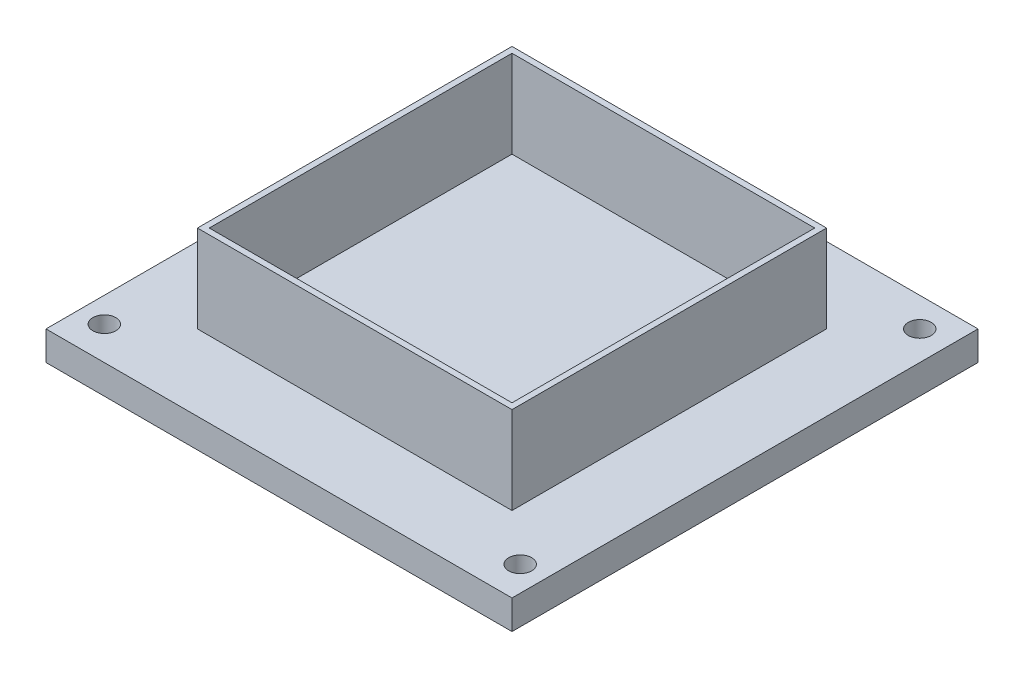
SolidWorks part; units mm, degrees
material "ABS_rapid_prototype"
ref_plane "Front" through (0, 0, 0) normal (0, 0, 1) x (1, 0, 0)
ref_plane "Top" through (0, 0, 0) normal (0, 1, 0) x (1, 0, 0)
ref_plane "Right" through (0, 0, 0) normal (1, 0, 0) x (0, 0, -1)
sketch "Sketch1" plane through (0, 0, 0) normal (0, 1, 0) x (1, 0, 0)
  line L1 (-50.8, 50.8) -> (50.8, 50.8)
  line L2 (-50.8, 50.8) -> (-50.8, -50.8)
  line L3 (-50.8, -50.8) -> (50.8, -50.8)
  line L4 (50.8, 50.8) -> (50.8, -50.8)
  line L5 (-50.8, 50.8) -> (50.8, -50.8) construction
  line L6 (-50.8, -50.8) -> (50.8, 50.8) construction
  line L7 (-38.1, 38.1) -> (38.1, 38.1)
  line L8 (-38.1, 38.1) -> (-38.1, -38.1)
  line L9 (-38.1, -38.1) -> (38.1, -38.1)
  line L10 (38.1, 38.1) -> (38.1, -38.1)
  line L11 (-38.1, 38.1) -> (38.1, -38.1) construction
  line L12 (-38.1, -38.1) -> (38.1, 38.1) construction
  line L13 (-34.29, 34.29) -> (34.29, 34.29)
  line L14 (-34.29, 34.29) -> (-34.29, -34.29)
  line L15 (-34.29, -34.29) -> (34.29, -34.29)
  line L16 (34.29, 34.29) -> (34.29, -34.29)
  line L17 (-34.29, 34.29) -> (34.29, -34.29) construction
  line L18 (-34.29, -34.29) -> (34.29, 34.29) construction
  line L19 (-33, 33) -> (33, 33)
  line L20 (-33, 33) -> (-33, -33)
  line L21 (-33, -33) -> (33, -33)
  line L22 (33, 33) -> (33, -33)
  line L23 (-33, 33) -> (33, -33) construction
  line L24 (-33, -33) -> (33, 33) construction
  point P0 (0, 0)
  point P5 (0, 0)
  point P11 (0, 0)
  point P16 (0, 0)
  dimension "D1" = 101.6
  dimension "D2" = 76.2
  dimension "D3" = 68.58
  dimension "D4" = 66
extrude "Boss-Extrude1" add sketch "Sketch1" along normal blind 25.4 contours L16 L13 L14 L15 L19 L22 L21 L20
sketch "Sketch2" plane through (0, 0, 0) normal (0, 1, 0) x (1, 0, 0)
  line L1 (-50.8, 50.8) -> (50.8, 50.8)
  line L2 (-50.8, 50.8) -> (-50.8, -50.8)
  line L3 (-50.8, -50.8) -> (50.8, -50.8)
  line L4 (50.8, 50.8) -> (50.8, -50.8)
  line L5 (-50.8, 50.8) -> (50.8, -50.8) construction
  line L6 (-50.8, -50.8) -> (50.8, 50.8) construction
  line L7 (-34.29, -34.29) -> (34.29, -34.29)
  line L8 (-34.29, -34.29) -> (-34.29, 34.29)
  line L9 (-34.29, 34.29) -> (34.29, 34.29)
  line L10 (34.29, -34.29) -> (34.29, 34.29)
  line L11 (-34.29, -34.29) -> (34.29, 34.29) construction
  line L12 (-34.29, 34.29) -> (34.29, -34.29) construction
  point P0 (0, 0)
  point P5 (0, 0)
extrude "Boss-Extrude2" add sketch "Sketch2" along normal blind 6.35 contours L2 L1 L4 L3
sketch "Sketch3" plane through (0, 6.35, 0) normal (0, 1, 0) x (1, 0, 0)
  line L0 (-50.8, 50.8) -> (50.8, 50.8) construction
  line L1 (-50.8, 50.8) -> (-50.8, -50.8) construction
  line L2 (0, 0) -> (0, 60.2924) construction
  circle A0 centre (-44.45, 44.45) radius 2.5
  circle A1 centre (-45.3318, -43.5504) radius 2.5
  circle A2 centre (45.3318, -43.5504) radius 2.5
  circle A3 centre (44.45, 44.45) radius 2.5
  dimension "D1" = 5
  dimension "D2" = 6.35
  dimension "D3" = 6.35
extrude "Cut-Extrude1" cut sketch "Sketch3" against normal through all
